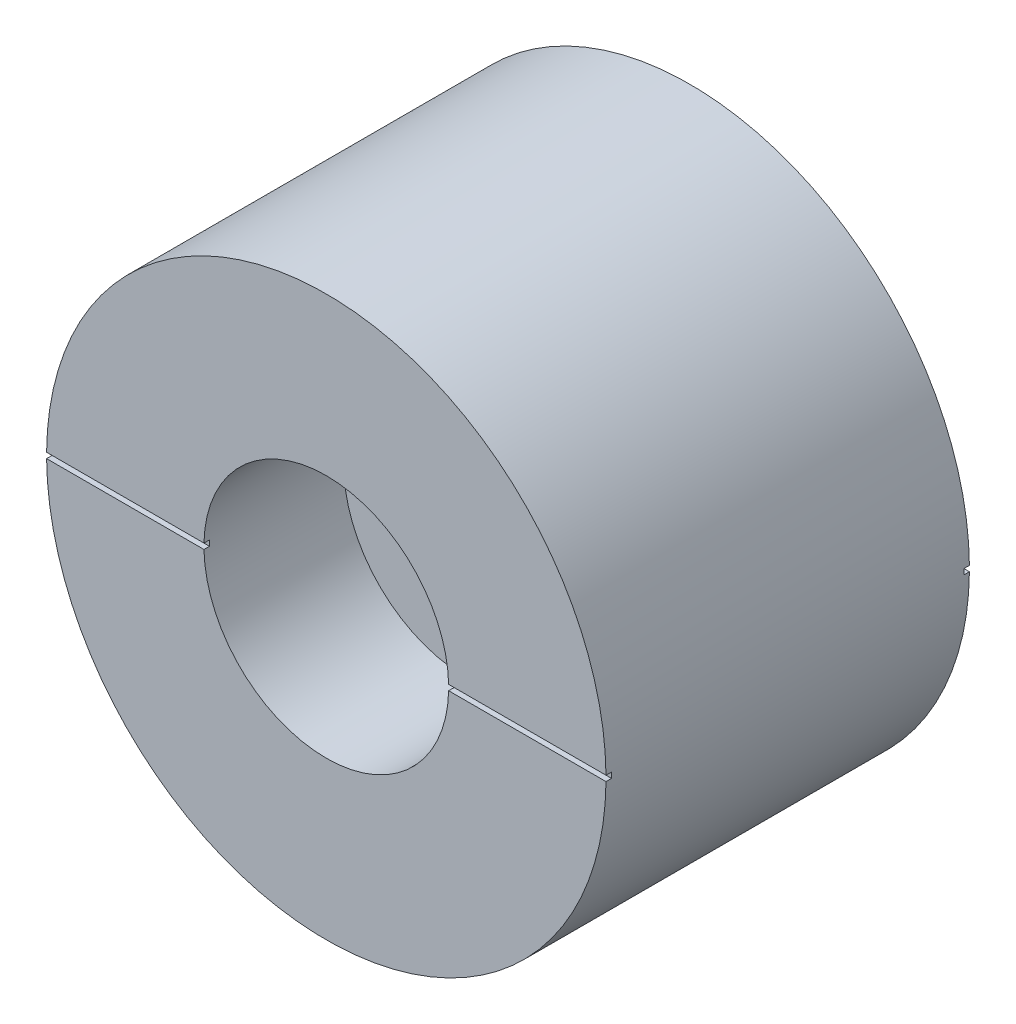
SolidWorks part; units mm, degrees
ref_plane "Front" through (0, 0, 0) normal (0, 0, 1) x (1, 0, 0)
ref_plane "Top" through (0, 0, 0) normal (0, 1, 0) x (1, 0, 0)
ref_plane "Right" through (0, 0, 0) normal (1, 0, 0) x (0, 0, -1)
sketch "Sketch1" plane through (0, 0, 0) normal (0, 0, 1) x (1, 0, 0)
  circle A0 centre (0, 0) radius 12.7
  dimension "D1" = 25.4
extrude "Base-Extrude" add sketch "Sketch1" along normal blind 16.5
hole_wizard "CBORE for 1/4 Socket Head Cap Screw1" positions "Sketch3" profile "Sketch2" counterbore size "1/4" standard "Ansi Inch" end condition through all
sketch "Sketch3" plane through (7.4603, -0.5046, 16.5) normal (0, 0, 1) x (1, 0, 0)
  point P0 (-7.4603, 0.5046)
sketch "Sketch2" plane through (0, 0, 16.5) normal (1, 0, 0) x (0, -1, 0)
  line L0 (0, 0) -> (0, 16.5)
  line L1 (0, 16.5) -> (3.2639, 16.5)
  line L3 (3.2639, 16.5) -> (3.2639, 6.35)
  line L4 (3.2639, 6.35) -> (5.5562, 6.35)
  line L5 (5.5562, 6.35) -> (5.5562, 0)
  line L7 (5.5562, 0) -> (0, 0)
  line L11 (0, -6.35) -> (0, 107.95) construction
  dimension "Thru Hole Dia." = 6.5278
  dimension "Thru Hole Depth" = 16.5
  dimension "C'Bore Dia." = 11.1125
  dimension "C'Bore Depth" = 6.35
sketch "Sketch4" plane through (0, 0, 16.5) normal (0, 0, 1) x (1, 0, 0)
  line L0 (-1.2513, 0) -> (1.6815, 0) construction
  line L1 (-13.178, 0.125) -> (13.7645, 0.125)
  line L2 (-13.178, 0.125) -> (-13.178, -0.125)
  line L3 (-13.178, -0.125) -> (13.7645, -0.125)
  line L4 (13.7645, 0.125) -> (13.7645, -0.125)
  dimension "D1" = 0.25
extrude "Vent Groove Front" cut sketch "Sketch4" against normal blind 0.25
sketch "Sketch5" plane through (0, 0, 0) normal (0, 0, -1) x (-1, 0, 0)
  line L0 (-1.5641, 0) -> (2.268, 0) construction
  line L1 (-13.4908, 0.125) -> (13.9991, 0.125)
  line L2 (-13.4908, 0.125) -> (-13.4908, -0.125)
  line L3 (-13.4908, -0.125) -> (13.9991, -0.125)
  line L4 (13.9991, 0.125) -> (13.9991, -0.125)
  dimension "D1" = 0.25
extrude "Vent Groove Back" cut sketch "Sketch5" against normal blind 0.25
